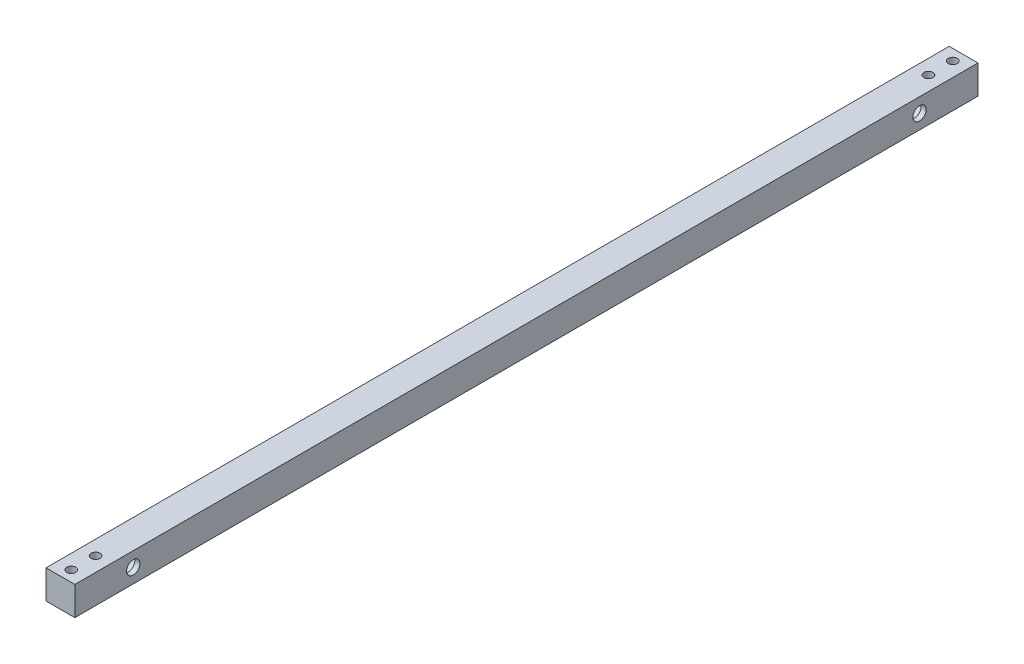
SolidWorks part; units mm, degrees
ref_plane "Front Plane" through (0, 0, 0) normal (0, 0, 1) x (1, 0, 0)
ref_plane "Top Plane" through (0, 0, 0) normal (0, 1, 0) x (1, 0, 0)
ref_plane "Right Plane" through (0, 0, 0) normal (1, 0, 0) x (0, 0, -1)
sketch "Sketch1" plane through (0, 0, 0) normal (0, 0, 1) x (1, 0, 0)
  line L1 (0, 0) -> (15.875, 0)
  line L2 (0, 0) -> (0, 15.875)
  line L3 (0, 15.875) -> (15.875, 15.875)
  line L4 (15.875, 0) -> (15.875, 15.875)
  dimension "D1" = 15.875
  dimension "D2" = 15.875
extrude "Boss-Extrude1" add sketch "Sketch1" along normal blind 497.84
sketch "Sketch8" plane through (0, 0, 0) normal (-1, 0, 0) x (0, 0, 1)
  line L0 (497.84, 7.9375) -> (0, 7.9375) construction
  line L1 (497.84, 15.875) -> (497.84, 0) construction
  line L2 (0, 15.875) -> (0, 0) construction
  line L3 (248.92, 15.875) -> (248.92, 0) construction
  line L4 (497.84, 15.875) -> (0, 15.875) construction
  line L5 (497.84, 0) -> (0, 0) construction
  circle A0 centre (465.6201, 7.9375) radius 6.8199
  circle A1 centre (32.2199, 7.9375) radius 6.8199
  dimension "D1" = 32.2199
extrude "Cut-Extrude1" cut sketch "Sketch8" against normal blind 13.0861
hole_wizard "L (0.29) Diameter Hole1" positions "Sketch10" profile "Sketch9" hole size "L" standard "ANSI Inch"
sketch "Sketch10" plane through (13.0861, 0, 0) normal (-1, 0, 0) x (0, 0, 1)
  point P0 (32.2199, 7.9375)
  point P3 (465.6201, 7.9375)
sketch "Sketch9" plane through (13.0861, 7.9375, 32.2199) normal (0, 1, 0) x (0, 0, 1)
  line L0 (0, 0) -> (0, 53.013)
  line L1 (0, 53.013) -> (3.683, 50.8)
  line L2 (3.683, 50.8) -> (3.683, 0)
  line L5 (3.683, 0) -> (0, 0)
  line L10 (0, 53.013) -> (-3.683, 50.8) construction
  line L11 (0, -6.35) -> (0, 107.95) construction
  dimension "Hole Dia." = 7.366
  dimension "Hole Depth" = 50.8
  dimension "Drill Angle" = 118
hole_wizard "CBORE for #10 Socket Head Cap Screw1" positions "Sketch11" profile "Sketch12" counterbore size "#10" standard "ANSI Inch"
sketch "Sketch11" plane through (-863.7241, 0, -1707.9731) normal (0, -1, 0) x (-1, 0, 0)
  point P0 (-404.9366, -2199.8131)
  point P3 (-404.9366, -2186.4131)
  point P6 (-871.6616, -2186.4131)
  point P9 (-871.6616, -2199.8131)
sketch "Sketch12" plane through (-458.7875, 0, 491.84) normal (1, 0, 0) x (0, 0, -1)
  line L0 (0, 0) -> (0, 26.8957)
  line L1 (0, 26.8957) -> (2.4892, 25.4)
  line L2 (2.4892, 25.4) -> (2.4892, 4.826)
  line L3 (2.4892, 4.826) -> (4.7625, 4.826)
  line L4 (4.7625, 4.826) -> (4.7625, 0)
  line L5 (4.7625, 0) -> (0, 0)
  line L6 (0, 26.8957) -> (-2.4892, 25.4) construction
  line L7 (0, -6.35) -> (0, 107.95) construction
  dimension "Hole Dia." = 4.9784
  dimension "Hole Depth" = 25.4
  dimension "C'Bore Dia." = 9.525
  dimension "C'Bore Depth" = 4.826
  dimension "Drill Angle" = 118
hole_wizard "CBORE for #10 Socket Head Cap Screw2" positions "Sketch13" profile "Sketch14" counterbore size "#10" standard "ANSI Inch"
sketch "Sketch13" plane through (-863.7241, 0, -1707.9731) normal (0, -1, 0) x (-1, 0, 0)
  point P0 (-404.9366, -1713.9731)
  point P3 (-404.9366, -1727.3731)
  point P6 (-871.6616, -1713.9731)
  point P9 (-871.6616, -1727.3731)
sketch "Sketch14" plane through (-458.7875, 0, 6) normal (1, 0, 0) x (0, 0, -1)
  line L0 (0, 0) -> (0, 26.8957)
  line L1 (0, 26.8957) -> (2.4892, 25.4)
  line L2 (2.4892, 25.4) -> (2.4892, 4.826)
  line L3 (2.4892, 4.826) -> (4.7625, 4.826)
  line L4 (4.7625, 4.826) -> (4.7625, 0)
  line L5 (4.7625, 0) -> (0, 0)
  line L6 (0, 26.8957) -> (-2.4892, 25.4) construction
  line L7 (0, -6.35) -> (0, 107.95) construction
  dimension "Hole Dia." = 4.9784
  dimension "Hole Depth" = 25.4
  dimension "C'Bore Dia." = 9.525
  dimension "C'Bore Depth" = 4.826
  dimension "Drill Angle" = 118
